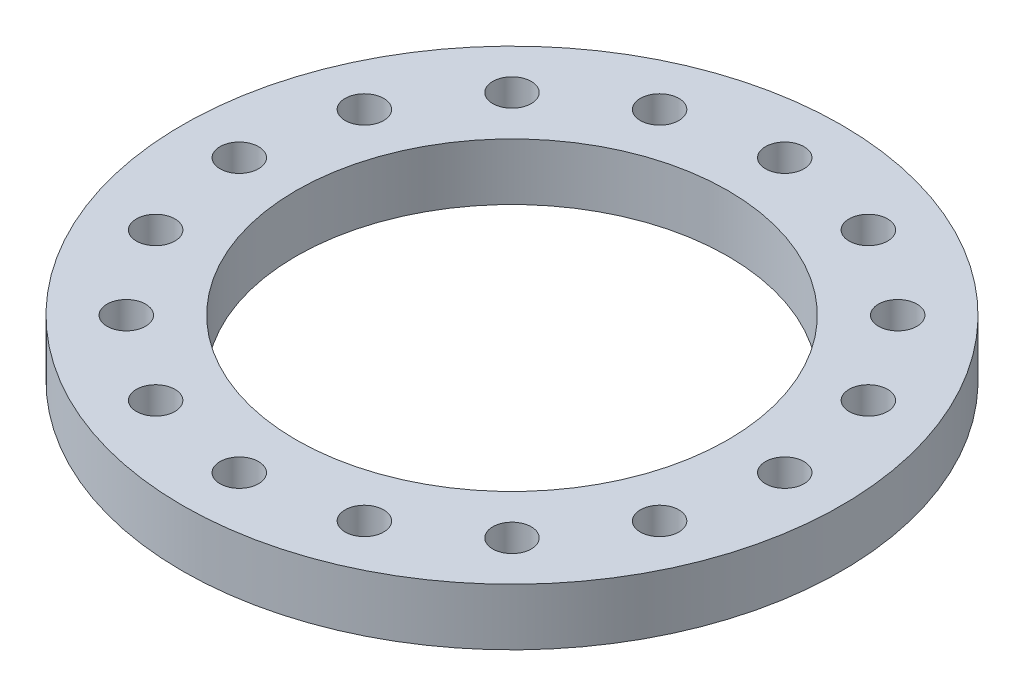
SolidWorks part; units mm, degrees
material "AISI 316 Stainless Steel Sheet (SS)"
ref_plane "Front Plane" through (0, 0, 0) normal (0, 0, 1) x (1, 0, 0)
ref_plane "Top Plane" through (0, 0, 0) normal (0, 1, 0) x (1, 0, 0)
ref_plane "Right Plane" through (0, 0, 0) normal (1, 0, 0) x (0, 0, -1)
sketch "Sketch1" plane through (0, 0, 0) normal (0, 1, 0) x (1, 0, 0)
  line L0 (0, 30.48) -> (0, 0) construction
  circle A0 centre (0, 0) radius 24.13
  circle A1 centre (0, 0) radius 36.83
  circle A3 centre (0, 30.48) radius 2.1526
  circle A4 centre (11.6642, 28.1598) radius 2.1527
  circle A5 centre (21.5526, 21.5526) radius 2.1526
  circle A6 centre (28.1598, 11.6642) radius 2.1527
  circle A7 centre (30.48, 0) radius 2.1527
  circle A8 centre (28.1598, -11.6642) radius 2.1527
  circle A9 centre (21.5526, -21.5526) radius 2.1526
  circle A10 centre (11.6642, -28.1598) radius 2.1526
  circle A11 centre (0, -30.48) radius 2.1526
  circle A12 centre (-11.6642, -28.1598) radius 2.1527
  circle A13 centre (-21.5526, -21.5526) radius 2.1526
  circle A14 centre (-28.1598, -11.6642) radius 2.1527
  circle A15 centre (-30.48, 0) radius 2.1527
  circle A16 centre (-28.1598, 11.6642) radius 2.1527
  circle A17 centre (-21.5526, 21.5526) radius 2.1526
  circle A18 centre (-11.6642, 28.1598) radius 2.1527
  point P40 (0, 0)
  dimension "D1" = 48.26
  dimension "D2" = 12.7
  dimension "D3" = 4.3053
  dimension "D5" = 30.48
  dimension "D4" = 16
extrude "Boss-Extrude1" add sketch "Sketch1" along normal blind 6.35
